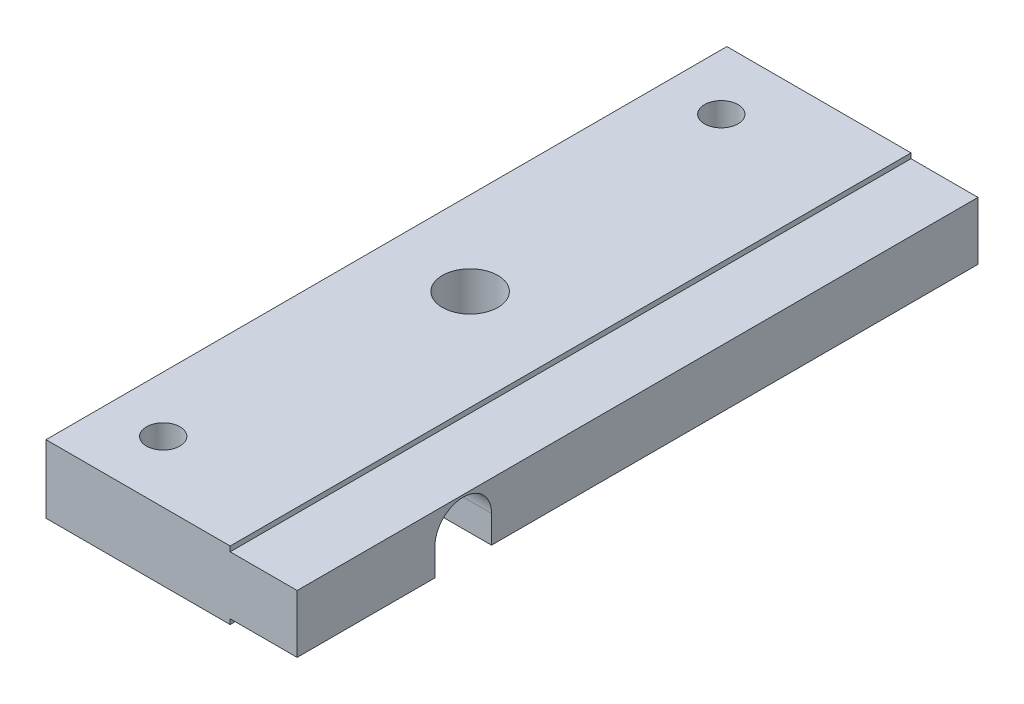
SolidWorks part; units mm, degrees
material "Generic Carbon Fiber"
ref_plane "Front Plane" through (0, 0, 0) normal (0, 0, 1) x (1, 0, 0)
ref_plane "Top Plane" through (0, 0, 0) normal (0, 1, 0) x (1, 0, 0)
ref_plane "Right Plane" through (0, 0, 0) normal (1, 0, 0) x (0, 0, -1)
sketch "Sketch1" plane through (0, 0, 0) normal (1, 0, 0) x (0, 0, -1)
  line L1 (0, -3.05) -> (61, -3.05)
  line L2 (0, -3.05) -> (0, 3.05)
  line L3 (0, 3.05) -> (61, 3.05)
  line L4 (61, -3.05) -> (61, 3.05)
  dimension "D1" = 61
  dimension "D2" = 6.1
extrude "Boss-Extrude1" add sketch "Sketch1" along normal blind 22.5
sketch "Sketch2" plane through (22.5, 0, 0) normal (1, 0, 0) x (0, 0, -1)
  line L0 (0, 3.05) -> (0, -3.05) construction
  line L1 (0, -2.5976) -> (61, -2.5976)
  line L2 (0, -2.5976) -> (0, 2.5976)
  line L3 (0, 2.5976) -> (61, 2.5976)
  line L4 (61, -2.5976) -> (61, 2.5976)
  line L5 (61, -3.05) -> (61, 3.05) construction
  line L7 (30.5, 3.05) -> (30.5, -3.05) construction
  line L8 (61, 3.05) -> (0, 3.05) construction
  line L9 (0, -3.05) -> (61, -3.05) construction
  line L10 (0, 0) -> (30.5, 0) construction
  dimension "D1" = 5.1952
extrude "Cut-Extrude1" cut sketch "Sketch2" against normal blind 6 flip side to cut
sketch "Sketch5" plane through (0, 0, 0) normal (-1, 0, 0) x (0, 0, 1)
  line L0 (-14.881, -0.1278) -> (0, -0.1278) construction
  line L1 (-61, 2.5976) -> (0, 2.5976) construction
  line L2 (0, 3.05) -> (0, -3.05) construction
  line L3 (0, -3.05) -> (-61, -3.05) construction
  line L4 (-12.3486, -0.1278) -> (-12.3486, -3.05)
  line L5 (-12.3486, -3.05) -> (-17.4134, -3.05)
  line L6 (-17.4134, -3.05) -> (-17.4134, -0.1278)
  arc A0 (-12.3486, -0.1278) -> (-17.4134, -0.1278) centre (-14.881, -0.1278) ccw
  dimension "D1" = 5.0648
  dimension "D2" = 14.881
  dimension "D3" = 2.7254
extrude "Cut-Extrude3" cut sketch "Sketch5" against normal through all
sketch "Sketch6" plane through (0, 3.05, 0) normal (0, 1, 0) x (1, 0, 0)
  line L0 (0, 30.5) -> (22.5, 30.5) construction
  line L2 (22.5, 61) -> (22.5, 0) construction
  line L3 (0, 61) -> (0, 0) construction
  line L4 (0, 61) -> (0, 0) construction
  circle A0 centre (7.5, 30.5) radius 2.4892
  dimension "D2" = 4.9784
  dimension "D1" = 7.5
extrude "Cut-Extrude4" cut sketch "Sketch6" against normal through all
sketch "Sketch7" plane through (0, 3.05, 0) normal (0, 1, 0) x (1, 0, 0)
  line L0 (5, 61) -> (5, 0) construction
  line L1 (16.5, 61) -> (0, 61) construction
  line L2 (16.5, 0) -> (0, 0) construction
  line L3 (0, 30.5) -> (22.5, 30.5) construction
  line L4 (0, 61) -> (0, 0) construction
  line L5 (22.5, 61) -> (22.5, 0) construction
  circle A0 centre (5, 55.5) radius 1.5
  circle A1 centre (5, 5.5) radius 1.5
  dimension "D1" = 3
  dimension "D2" = 5
  dimension "D3" = 25
  dimension "D4" = 25
extrude "Cut-Extrude5" cut sketch "Sketch7" against normal through all
